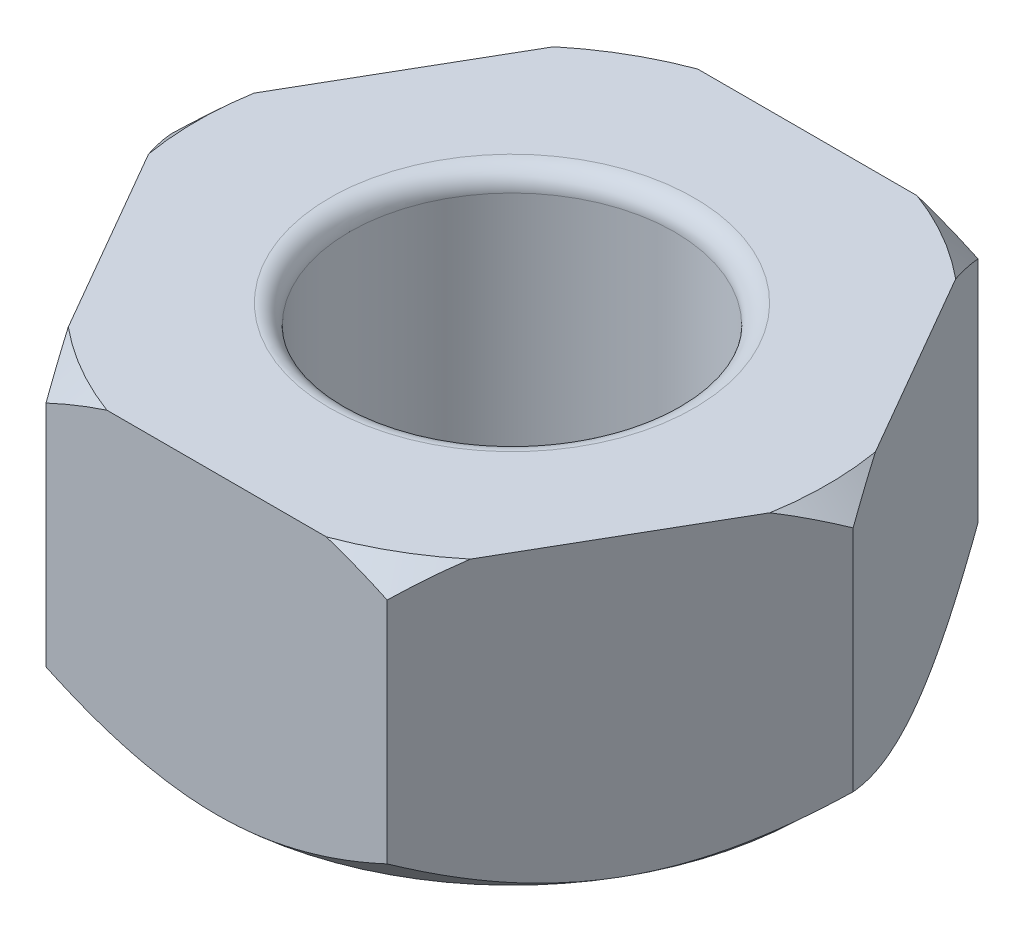
SolidWorks part; units mm, degrees
ref_plane "Alzado" through (0, 0, 0) normal (0, 0, 1) x (1, 0, 0)
ref_plane "Planta" through (0, 0, 0) normal (0, 1, 0) x (1, 0, 0)
ref_plane "Vista lateral" through (0, 0, 0) normal (1, 0, 0) x (0, 0, -1)
sketch "Croquis1" plane through (0, 0, 0) normal (0, 1, 0) x (1, 0, 0)
  line L0 (0, 20.3129) -> (0, -20.6756) construction
  line L2 (17.3205, 0) -> (8.6603, 15)
  line L3 (8.6603, 15) -> (-8.6603, 15)
  line L4 (-8.6603, 15) -> (-17.3205, 0)
  line L5 (-17.3205, 0) -> (-8.6603, -15)
  line L6 (-8.6603, -15) -> (8.6603, -15)
  line L7 (8.6603, -15) -> (17.3205, 0)
  circle A0 centre (0, 0) radius 18.4752
  circle A1 centre (0, 0) radius 15 construction
  dimension "D1" = 30
extrude "Saliente-Extruir1" add sketch "Croquis1" against normal blind 15 contours L6 L7 L2 L3 L4 L5
sketch "Croquis2" plane through (0, 0, 0) normal (0, 1, 0) x (1, 0, 0)
  circle A0 centre (0, 0) radius 16
extrude "Cortar-Extruir1" cut sketch "Croquis2" against normal blind 15 draft 47 flip side to cut
sketch "Croquis3" plane through (0, -15, 0) normal (0, -1, 0) x (1, 0, 0)
  circle A0 centre (0, 0) radius 15
  dimension "D1" = 30
extrude "Cortar-Extruir2" cut sketch "Croquis3" against normal blind 15 draft 47 flip side to cut
sketch "Croquis4" plane through (0, 0, 0) normal (0, 1, 0) x (1, 0, 0)
  circle A0 centre (0, 0) radius 8.25
  dimension "D1" = 16.5
extrude "Cortar-Extruir3" cut sketch "Croquis4" against normal blind 15
fillet "Redondeo1" radius 1 2 edges at (0, -15, 8.25) (0, 0, 8.25)
